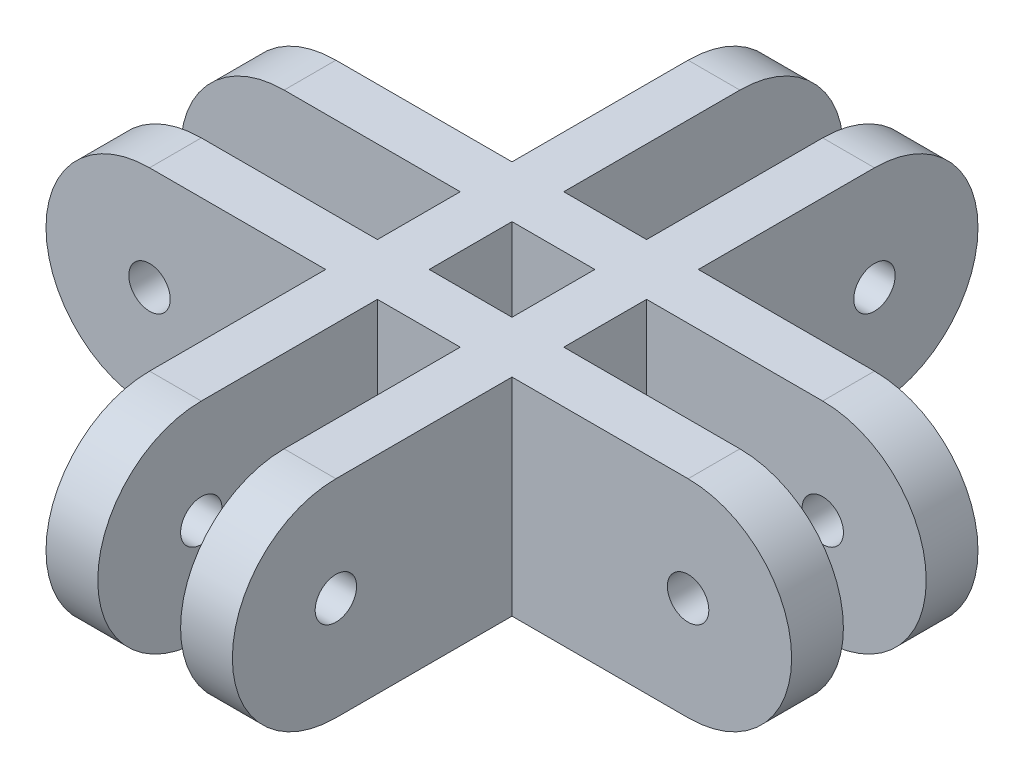
SolidWorks part; units mm, degrees
ref_plane "Alzado" through (0, 0, 0) normal (0, 0, 1) x (1, 0, 0)
ref_plane "Planta" through (0, 0, 0) normal (0, 1, 0) x (1, 0, 0)
ref_plane "Vista lateral" through (0, 0, 0) normal (1, 0, 0) x (0, 0, -1)
sketch "Croquis1" plane through (0, 0, 0) normal (0, 0, 1) x (1, 0, 0)
  line L0 (-26.01, -10) -> (-26.01, 10)
  line L2 (0, 10) -> (-52.02, 10)
  line L3 (0, -10) -> (-52.02, -10)
  arc A0 (0, -10) -> (0, 10) centre (0, 0) ccw
  circle A1 centre (0, 0) radius 2
  circle A2 centre (-52.02, 0) radius 2
  arc A3 (-52.02, -10) -> (-52.02, 10) centre (-52.02, 0) cw
extrude "Saliente-Extruir1" add sketch "Croquis1" along normal blind 5 contours A3 L3 L0 L2 A2 | L3 A0 L2 L0 A1
sketch "Croquis2" plane through (0, 10, 0) normal (0, 1, 0) x (1, 0, 0)
  line L0 (0, -5) -> (0, -13)
  line L1 (0, -5) -> (-52.02, -5) construction
  dimension "D1" = 8
ref_plane "Plano1" through (0, 0, 13) normal (0, 0, 1) x (1, 0, 0)
sketch "Croquis3" plane through (0, 0, 13) normal (0, 0, 1) x (1, 0, 0)
  line L0 (-52.02, 10) -> (0, 10)
  line L1 (-52.02, -10) -> (0, -10)
  arc A0 (-52.02, -10) -> (-52.02, 10) centre (-52.02, 0) cw
  arc A1 (0, -10) -> (0, 10) centre (0, 0) ccw
  circle A2 centre (-52.02, 0) radius 2
  circle A3 centre (0, 0) radius 2
extrude "Saliente-Extruir2" add sketch "Croquis3" along normal blind 5 separate body
sketch "Croquis4" plane through (0, 10, 0) normal (0, 1, 0) x (1, 0, 0)
  line L1 (10, 0) -> (0, 0) construction
  line L3 (-17.01, 0) -> (10, 0)
  line L7 (0, 0) -> (-52.02, 0) construction
  line L8 (-62.02, 0) -> (-35.01, 0)
ref_plane "Plano2" through (-17.01, 10, 0) normal (1, 0, 0) x (0, 0, -1)
sketch "Croquis5" plane through (-17.01, 10, 0) normal (1, 0, 0) x (0, 0, -1)
  line L0 (-5, -10) -> (-13, -10)
  line L1 (-5, 0) -> (-5, -20) construction
  line L2 (-13, 1) -> (-13, -21) construction
  line L3 (-9, -10) -> (-9, 0)
  line L4 (-5, 0) -> (-13, 0) construction
  line L5 (-35.01, 0) -> (17.01, 0)
  line L6 (-5, -20) -> (-13, -20)
  line L7 (-9, -10) -> (-9, -20)
  line L8 (-5, -20) -> (17.01, -20)
  line L9 (17.01, 0) -> (17.01, -20)
  line L10 (-35.01, 0) -> (-35.01, -20)
  line L11 (-13, -20) -> (-35.01, -20)
  circle A0 centre (17.01, -10) radius 2
  arc A1 (17.01, -20) -> (17.01, 0) centre (17.01, -10) ccw
  arc A2 (-35.01, -20) -> (-35.01, 0) centre (-35.01, -10) cw
  circle A3 centre (-35.01, -10) radius 2
  dimension "D2" = 4
extrude "Saliente-Extruir3" add sketch "Croquis5" against normal blind 5
ref_plane "Plano3" through (-35.01, 10, 0) normal (1, 0, 0) x (0, 0, -1)
sketch "Croquis6" plane through (-35.01, 10, 0) normal (1, 0, 0) x (0, 0, -1)
  line L0 (-9, 0) -> (-9, -20)
  line L3 (-5, 0) -> (-13, 0) construction
  line L4 (-5, -20) -> (-13, -20) construction
  line L5 (-35.01, -20) -> (17.01, -20)
  line L6 (-35.01, 0) -> (17.01, 0)
  arc A0 (17.01, -20) -> (17.01, 0) centre (17.01, -10) ccw
  circle A1 centre (17.01, -10) radius 2
  arc A2 (-35.01, -20) -> (-35.01, 0) centre (-35.01, -10) cw
  circle A3 centre (-35.01, -10) radius 2
extrude "Saliente-Extruir4" add sketch "Croquis6" along normal blind 5 contours L5 A0 L6 L0 A1 | A2 L5 L0 L6 A3
